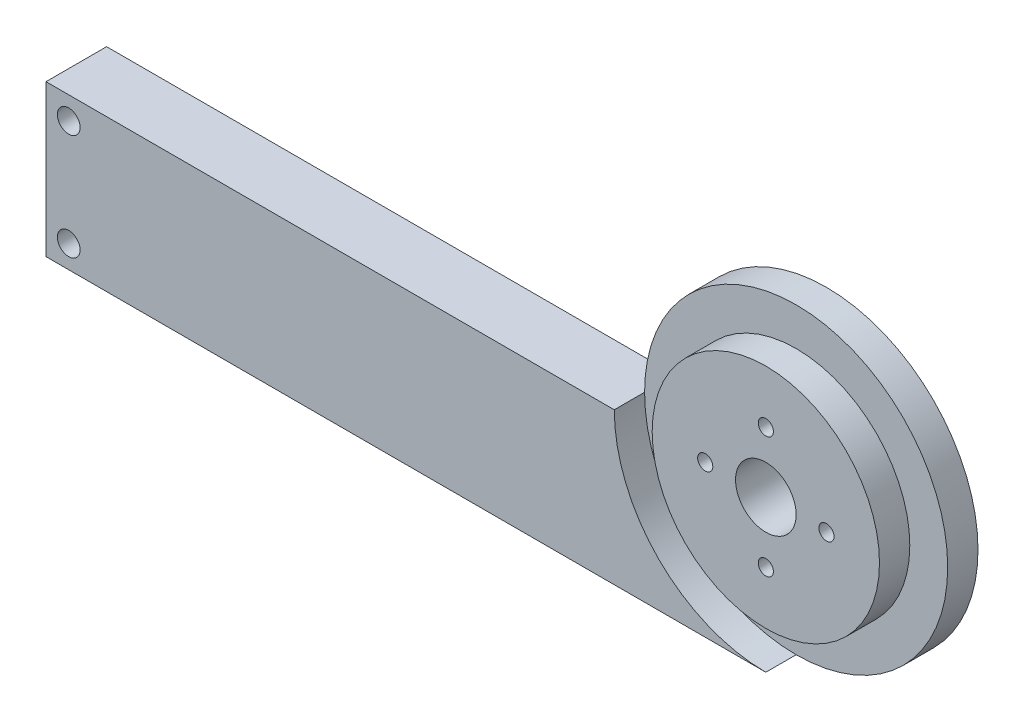
SolidWorks part; units mm, degrees
ref_plane "Plan de face" through (0, 0, 0) normal (0, 0, 1) x (1, 0, 0)
ref_plane "Plan de dessus" through (0, 0, 0) normal (0, 1, 0) x (1, 0, 0)
ref_plane "Plan de droite" through (0, 0, 0) normal (1, 0, 0) x (0, 0, -1)
sketch "Esquisse1" plane through (0, 0, 0) normal (0, 0, 1) x (1, 0, 0)
  line L1 (-45.5828, 28.0993) -> (32.9922, 28.0993)
  line L2 (-45.5828, 28.0993) -> (-45.5828, 8.0993)
  line L3 (-45.5828, 8.0993) -> (32.9922, 8.0993)
  line L4 (32.9922, 28.0993) -> (32.9922, 8.0993)
  circle A0 centre (32.9922, 28.0993) radius 20
  dimension "D3" = 40
  dimension "D1" = 0
  dimension "D2" = 20
  dimension "D4" = 0
extrude "Boss.-Extru.1" add sketch "Esquisse1" along normal blind 8 contours L4 A0 L1 | L1 A0 L4 | A0 L1 L2 L3
sketch "Esquisse4" plane through (0, 0, 8) normal (0, 0, 1) x (1, 0, 0)
  circle A0 centre (32.9922, 28.0993) radius 15
  arc A1 (32.9922, 8.0993) -> (12.9922, 28.0993) centre (32.9922, 28.0993) ccw construction
  circle A2 centre (32.9922, 28.0993) radius 20
  dimension "D1" = 0
extrude "Enlèv. mat.-Extru.2" cut sketch "Esquisse4" against normal blind 4
sketch "Esquisse5" plane through (0, 0, 8) normal (0, 0, 1) x (1, 0, 0)
  line L0 (-45.5828, 28.0993) -> (12.9922, 28.0993) construction
  line L1 (-45.5828, 8.0993) -> (-62.0028, 8.0993)
  line L2 (-45.5828, 8.0993) -> (-45.5828, 28.0993)
  line L3 (-45.5828, 28.0993) -> (-62.0028, 28.0993)
  line L4 (-62.0028, 8.0993) -> (-62.0028, 28.0993)
  dimension "D1" = 0
  dimension "D2" = 16.42
  dimension "D3" = 20
extrude "Boss.-Extru.2" add sketch "Esquisse5" against normal blind 8
sketch "Esquisse6" plane through (0, 0, 8) normal (0, 0, 1) x (1, 0, 0)
  circle A0 centre (32.9922, 28.0993) radius 8 construction
  circle A1 centre (32.9922, 28.0993) radius 15 construction
  circle A2 centre (32.9922, 28.0993) radius 4
  circle A3 centre (32.9922, 36.0993) radius 1
  circle A4 centre (40.9922, 28.0993) radius 1
  circle A5 centre (32.9922, 20.0993) radius 1
  circle A6 centre (24.9922, 28.0993) radius 1
  dimension "D1" = 0
  dimension "D2" = 2
  dimension "D3" = 2
  dimension "D4" = 2
  dimension "D5" = 2
  dimension "D6" = 0
extrude "Enlèv. mat.-Extru.3" cut sketch "Esquisse6" against normal blind 10 contours A5 | A4 | A6 | A3 | A2
sketch "Esquisse7" plane through (0, 0, 8) normal (0, 0, 1) x (1, 0, 0)
  line L0 (-62.0028, 28.0993) -> (12.9922, 28.0993) construction
  line L1 (-62.0028, 28.0993) -> (-62.0028, 8.0993) construction
  line L2 (-62.0028, 8.0993) -> (32.9922, 8.0993) construction
  circle A0 centre (-59.0028, 25.0993) radius 1.5
  circle A1 centre (-59.0028, 11.0993) radius 1.5
  dimension "D1" = 3
  dimension "D2" = 3
  dimension "D3" = 3
  dimension "D4" = 3
  dimension "D5" = 3
  dimension "D6" = 3
extrude "Enlèv. mat.-Extru.4" cut sketch "Esquisse7" against normal blind 10
sketch "Esquisse8" plane through (0, 0, 0) normal (0, 0, -1) x (-1, 0, 0)
  circle A0 centre (-32.9922, 28.0993) radius 20
  circle A2 centre (-32.9922, 28.0993) radius 15
